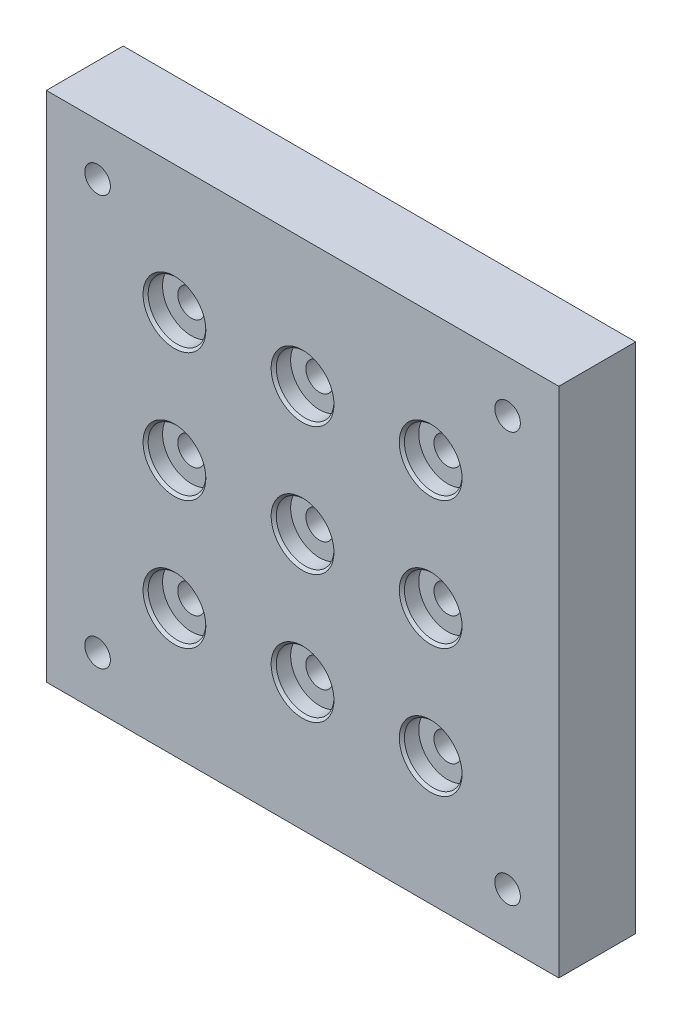
SolidWorks part; units mm, degrees
ref_plane "Front Plane" through (0, 0, 0) normal (0, 0, 1) x (1, 0, 0)
ref_plane "Top Plane" through (0, 0, 0) normal (0, 1, 0) x (1, 0, 0)
ref_plane "Right Plane" through (0, 0, 0) normal (1, 0, 0) x (0, 0, -1)
sketch "Sketch2" plane through (0, 0, 0) normal (0, 0, 1) x (1, 0, 0)
  line L1 (-63.5, -63.5) -> (63.5, -63.5)
  line L2 (-63.5, -63.5) -> (-63.5, 63.5)
  line L3 (-63.5, 63.5) -> (63.5, 63.5)
  line L4 (63.5, -63.5) -> (63.5, 63.5)
  line L5 (-63.5, -63.5) -> (63.5, 63.5) construction
  line L6 (-63.5, 63.5) -> (63.5, -63.5) construction
  point P0 (0, 0)
  dimension "D1" = 127
  dimension "D2" = 127
extrude "Boss-Extrude1" add sketch "Sketch2" along normal blind 19.05
hole_wizard "CBORE for 1/4 Binding Head Machine Screw1" positions "Sketch4" profile "Sketch5" counterbore size "1/4" standard "ANSI Inch" end condition through all
sketch "Sketch4" plane through (0, 0, 19.05) normal (0, 0, 1) x (1, 0, 0)
  point P0 (0, 0)
sketch "Sketch5" plane through (0, 0, 19.05) normal (1, 0, 0) x (0, -1, 0)
  line L0 (0, 0) -> (0, 19.05)
  line L1 (0, 19.05) -> (3.3782, 19.05)
  line L3 (3.3782, 19.05) -> (3.3782, 4.191)
  line L4 (7.1437, 4.191) -> (3.3782, 4.191)
  line L5 (7.1437, 4.191) -> (7.1437, 0.635)
  line L6 (7.1437, 0.635) -> (7.7788, 0)
  line L7 (7.7788, 0) -> (0, 0)
  line L8 (-7.1437, 0.635) -> (-7.7788, 0) construction
  line L11 (0, -6.35) -> (0, 107.95) construction
  dimension "Thru Hole Dia." = 6.7564
  dimension "Thru Hole Depth" = 19.05
  dimension "C'Bore Dia." = 14.2875
  dimension "C'Bore Depth" = 4.191
  dimension "Near C'Sink Dia." = 15.5575
  dimension "Near C'Sink Angle" = 90
pattern_linear "LPattern1" count 2 spacing 31.75 along (1, 0, 0) count 2 spacing 31.75 along (-1, 0, 0) of "CBORE for 1/4 Binding Head Machine Screw1"
pattern_linear "LPattern2" count 2 spacing 31.75 along (0, -1, 0) count 2 spacing 31.75 along (0, 1, 0) of "LPattern1", "CBORE for 1/4 Binding Head Machine Screw1"
hole_wizard "1/4 (0.25) Diameter Hole1" positions "Sketch7" profile "Sketch6" hole size "1/4" standard "ANSI Inch"
sketch "Sketch7" plane through (0, 0, 19.05) normal (0, 0, 1) x (1, 0, 0)
  point P0 (-50.8, 50.8)
  point P2 (50.8, 50.8)
  point P4 (50.8, -50.8)
  point P6 (-50.8, -50.8)
  dimension "D1" = 50.8
  dimension "D2" = 50.8
  dimension "D3" = 50.8
  dimension "D4" = 50.8
sketch "Sketch6" plane through (-50.8, 50.8, 19.05) normal (1, 0, 0) x (0, -1, 0)
  line L0 (0, 0) -> (0, 61.8517)
  line L1 (0, 61.8517) -> (3.175, 59.944)
  line L2 (3.175, 59.944) -> (3.175, 0)
  line L5 (3.175, 0) -> (0, 0)
  line L10 (0, 61.8517) -> (-3.175, 59.944) construction
  line L11 (0, -6.35) -> (0, 107.95) construction
  dimension "Hole Dia." = 6.35
  dimension "Hole Depth" = 59.944
  dimension "Drill Angle" = 118
